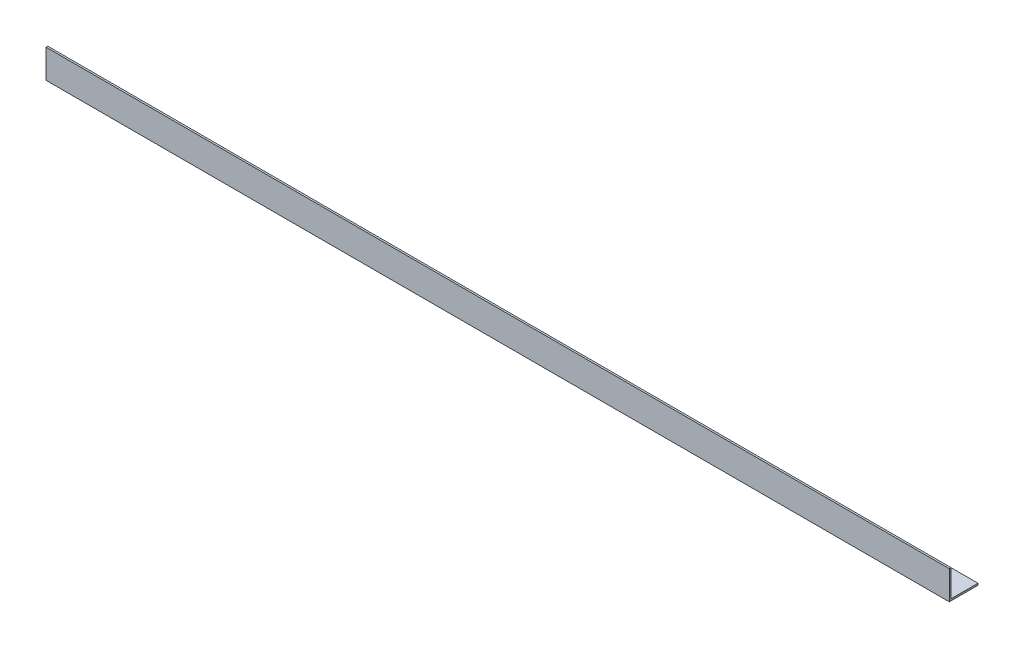
SolidWorks part; units mm, degrees
material "6061-T6 (SS)"
ref_plane "Front Plane" through (0, 0, 0) normal (0, 0, 1) x (1, 0, 0)
ref_plane "Top Plane" through (0, 0, 0) normal (0, 1, 0) x (1, 0, 0)
ref_plane "Right Plane" through (0, 0, 0) normal (1, 0, 0) x (0, 0, -1)
sketch "Sketch4" plane through (0, 0, 0) normal (1, 0, 0) x (0, 0, -1)
  line L0 (0, 0) -> (0, 25.4)
  line L1 (0, 0) -> (25.4, 0)
  line L2 (25.4, 0) -> (25.4, 1.5875)
  line L3 (25.4, 1.5875) -> (1.5875, 1.5875)
  line L4 (1.5875, 1.5875) -> (1.5875, 25.4)
  line L5 (1.5875, 25.4) -> (0, 25.4)
  dimension "D1" = 25.4
  dimension "D2" = 1.5875
extrude "Boss-Extrude1" add sketch "Sketch4" along normal blind 800.1
